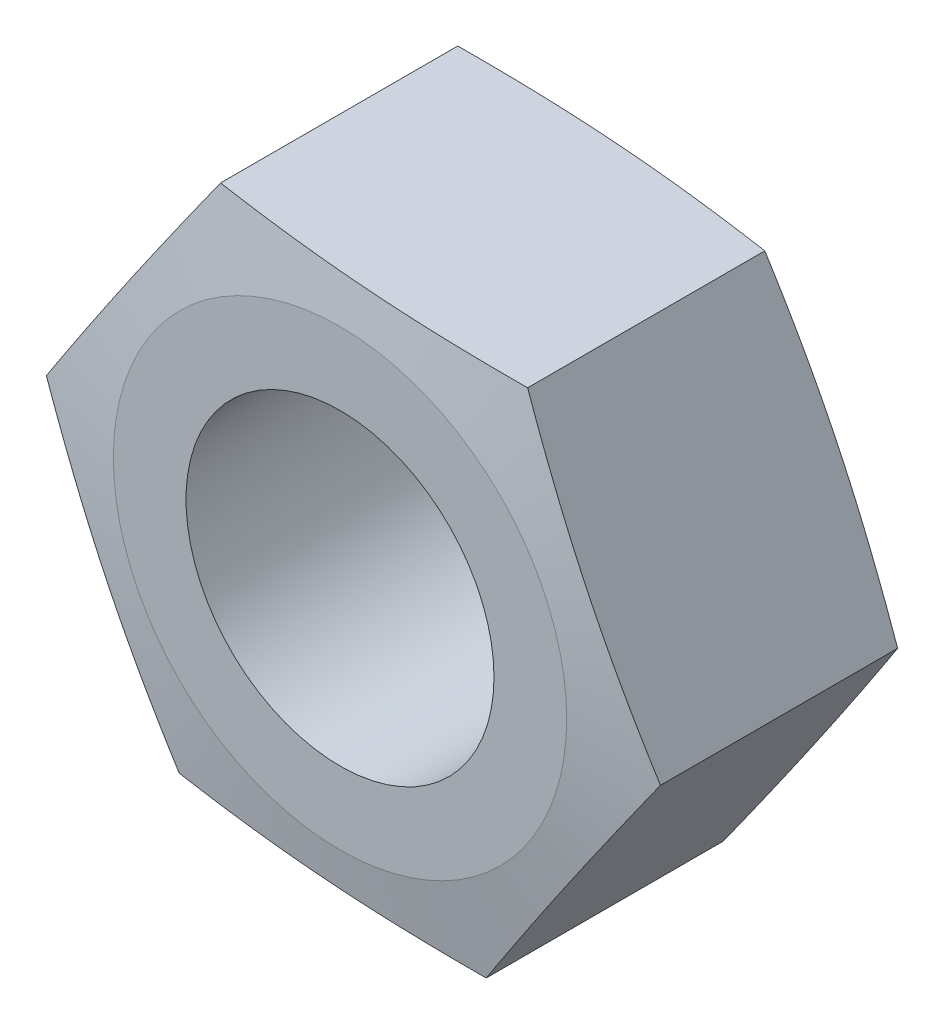
SolidWorks part; units mm, degrees
ref_plane "Спереди" through (0, 0, 0) normal (0, 0, 1) x (1, 0, 0)
ref_plane "Сверху" through (0, 0, 0) normal (0, 1, 0) x (1, 0, 0)
ref_plane "Справа" through (0, 0, 0) normal (1, 0, 0) x (0, 0, -1)
sketch "Эскиз1" plane through (0, 0, 0) normal (0, 0, 1) x (1, 0, 0)
  line L1 (-3.0192, 6.3154) -> (-6.9789, 0.543)
  line L2 (-6.9789, 0.543) -> (-3.9597, -5.7724)
  line L3 (-3.9597, -5.7724) -> (3.0192, -6.3154)
  line L4 (3.0192, -6.3154) -> (6.9789, -0.543)
  line L5 (6.9789, -0.543) -> (3.9597, 5.7724)
  line L6 (3.9597, 5.7724) -> (-3.0192, 6.3154)
  circle A1 centre (0, 0) radius 6.0622 construction
extrude "Вытянуть1" add sketch "Эскиз1" along normal blind 6
sketch "Эскиз3" plane through (0, 0, 0) normal (0, 0, -1) x (-1, 0, 0)
  circle A0 centre (0, 0) radius 4.8075
sketch "Эскиз4" plane through (0, 0, 0) normal (0, 1, 0) x (1, 0, 0)
  line L0 (-5.152, 0) -> (-8.0171, -0.4727)
  line L1 (-8.0171, -0.4727) -> (-8.0171, 0.6899)
  line L2 (-8.0171, 0.6899) -> (-5.152, 0)
sweep "Вырез-По траектории1" cut profiles "Эскиз4" path "Эскиз3"
ref_plane "Плоскость1" through (0, 0, 3) normal (0, 0, -1) x (-1, 0, 0)
mirror "Зеркальное отражение1" about plane through (0, 0, 3) normal (0, 0, -1) of "Вырез-По траектории1"
sketch "Эскиз5" plane through (0, 0, 6) normal (0, 0, 1) x (1, 0, 0)
  circle A0 centre (0, 0) radius 3.5
extrude "Вытянуть2" cut sketch "Эскиз5" against normal through all
cosmetic thread "Условное изображение резьбы1" parameters "D2"=7.5
cosmetic thread "Условное изображение резьбы2" parameters "D2"=7.5
chamfer "Фаска1" distance 0.5 angle 45 1 edges at (3.5, 0, 0)
